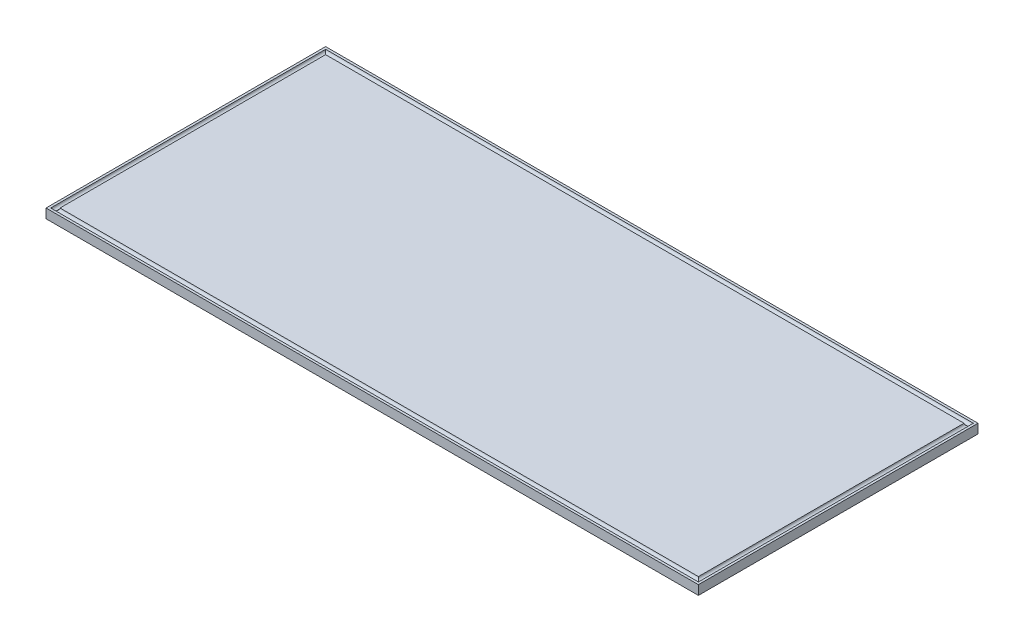
SolidWorks part; units mm, degrees
ref_plane "Front Plane" through (0, 0, 0) normal (0, 0, 1) x (1, 0, 0)
ref_plane "Top Plane" through (0, 0, 0) normal (0, 1, 0) x (1, 0, 0)
ref_plane "Right Plane" through (0, 0, 0) normal (1, 0, 0) x (0, 0, -1)
sketch "Sketch1" plane through (0, 0, 0) normal (0, 1, 0) x (1, 0, 0)
  line L1 (0, 0) -> (-140, 0)
  line L2 (0, 0) -> (0, -60)
  line L3 (0, -60) -> (-140, -60)
  line L4 (-140, 0) -> (-140, -60)
  dimension "D1" = 60
  dimension "D2" = 140
extrude "Boss-Extrude1" add sketch "Sketch1" along normal blind 2
sketch "Sketch2" plane through (0, 2, 0) normal (0, 1, 0) x (1, 0, 0)
  line L8 (-1, -59) -> (-1, -1)
  line L9 (-1, -1) -> (-139, -1)
  line L10 (-139, -1) -> (-139, -59)
  line L11 (-139, -59) -> (-1, -59)
  line L12 (-1, -59) -> (-1, -1)
  line L13 (-1, -1) -> (-139, -1)
  line L14 (-139, -1) -> (-139, -59)
  line L15 (-139, -59) -> (-1, -59)
  dimension "D1" = 1
sweep "Cut-Sweep1" cut path "Sketch2" circular profile diameter 1 parameters "D3"=1
